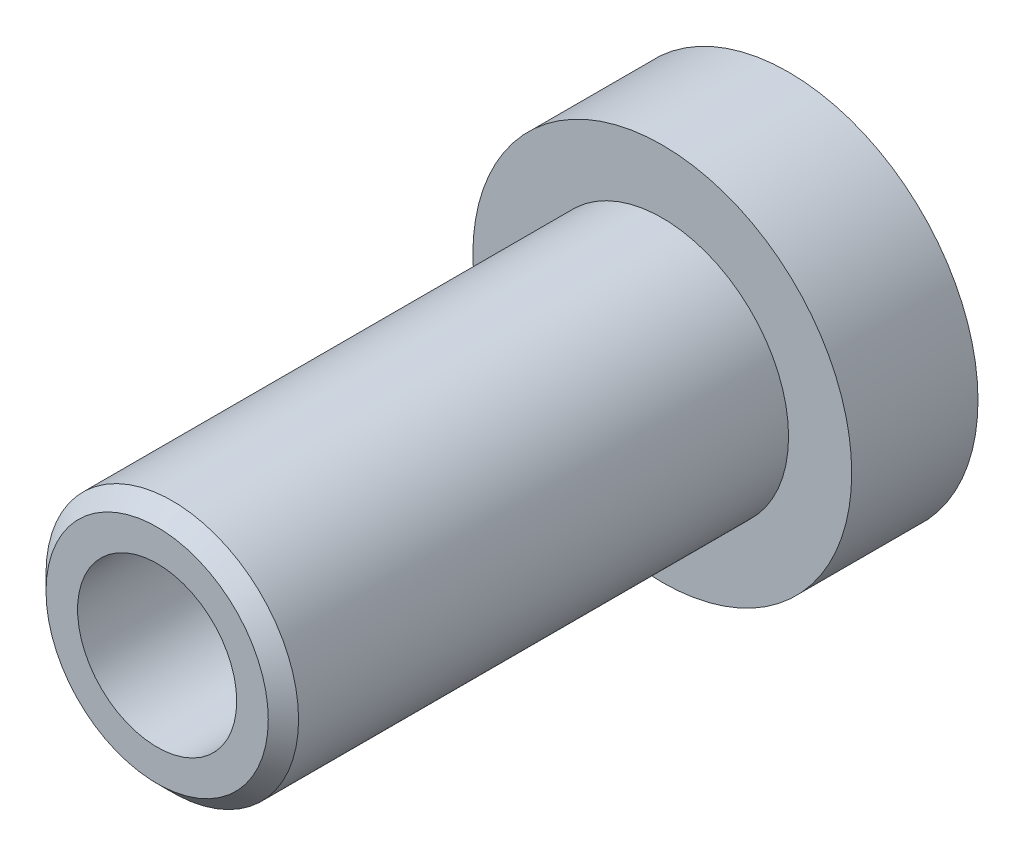
SolidWorks part; units mm, degrees
material "Cast Carbon Steel"
ref_plane "Front Plane" through (0, 0, 0) normal (0, 0, 1) x (1, 0, 0)
ref_plane "Top Plane" through (0, 0, 0) normal (0, 1, 0) x (1, 0, 0)
ref_plane "Right Plane" through (0, 0, 0) normal (1, 0, 0) x (0, 0, -1)
sketch "Sketch1" plane through (0, 0, 0) normal (0, 1, 0) x (1, 0, 0)
  line L0 (0, 73.76) -> (0, -176.24) construction
  line L1 (0, 73.76) -> (75, 73.76)
  line L2 (75, 73.76) -> (75, 23.76)
  line L3 (75, 23.76) -> (50, 23.76)
  line L4 (50, 23.76) -> (50, -170.24)
  line L5 (44, -176.24) -> (0, -176.24)
  line L6 (50, -170.24) -> (44, -176.24)
  line L7 (0, 73.76) -> (0, -176.24)
  point P7 (50, -176.24)
  dimension "D1" = 75
  dimension "D2" = 50
  dimension "D3" = 50
  dimension "D4" = 250
  dimension "D5" = 6
  dimension "D6" = 45
revolve "Revolve1" add sketch "Sketch1" angle 360 about L0
sketch "Sketch2" plane through (0, 0, 176.24) normal (0, 0, 1) x (1, 0, 0)
  circle A0 centre (0, 0) radius 31.5
  dimension "D1" = 63
extrude "Cut-Extrude1" cut sketch "Sketch2" against normal through all
